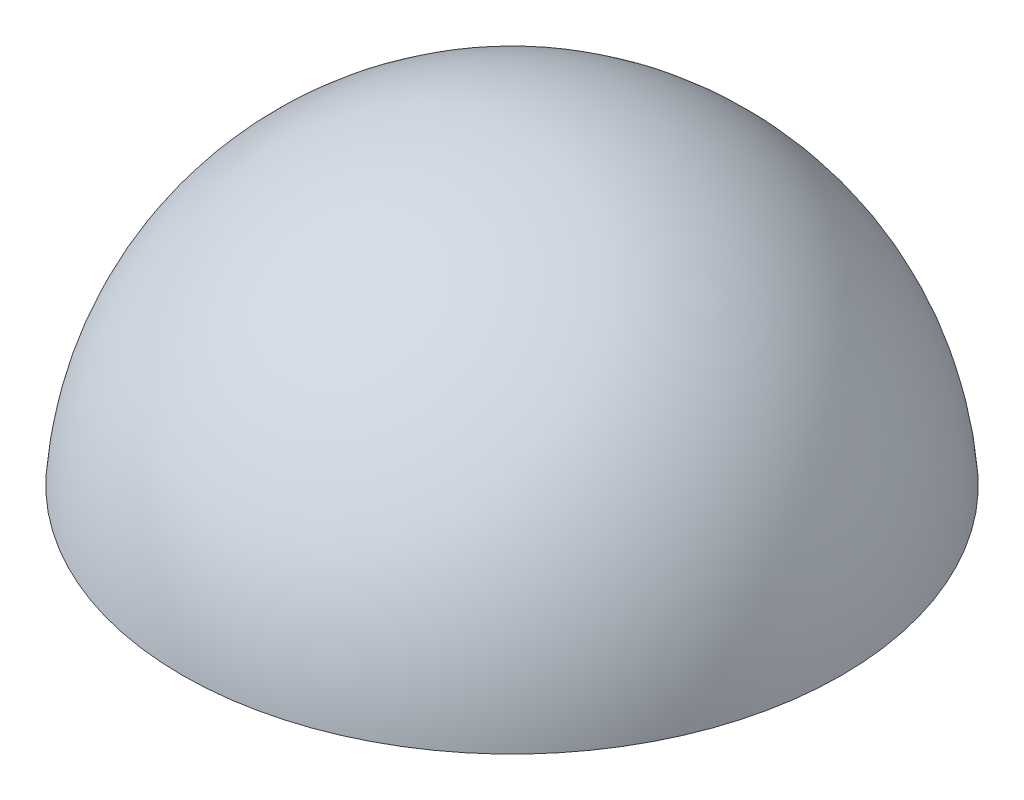
SolidWorks part; units mm, degrees
ref_plane "Front" through (0, 0, 0) normal (0, 0, 1) x (1, 0, 0)
ref_plane "Top" through (0, 0, 0) normal (0, 1, 0) x (1, 0, 0)
ref_plane "Right" through (0, 0, 0) normal (1, 0, 0) x (0, 0, -1)
sketch "Sketch1" plane through (0, 0, 0) normal (0, 0, 1) x (1, 0, 0)
  line L0 (-16.8355, 0) -> (16.8355, 0)
  line L1 (0, 0) -> (0, 15.6158) construction
  arc A0 (-16.8355, 0) -> (16.8355, 0) centre (0, -1.2673) cw
revolve "Revolve1" add sketch "Sketch1" angle 360 about L1
